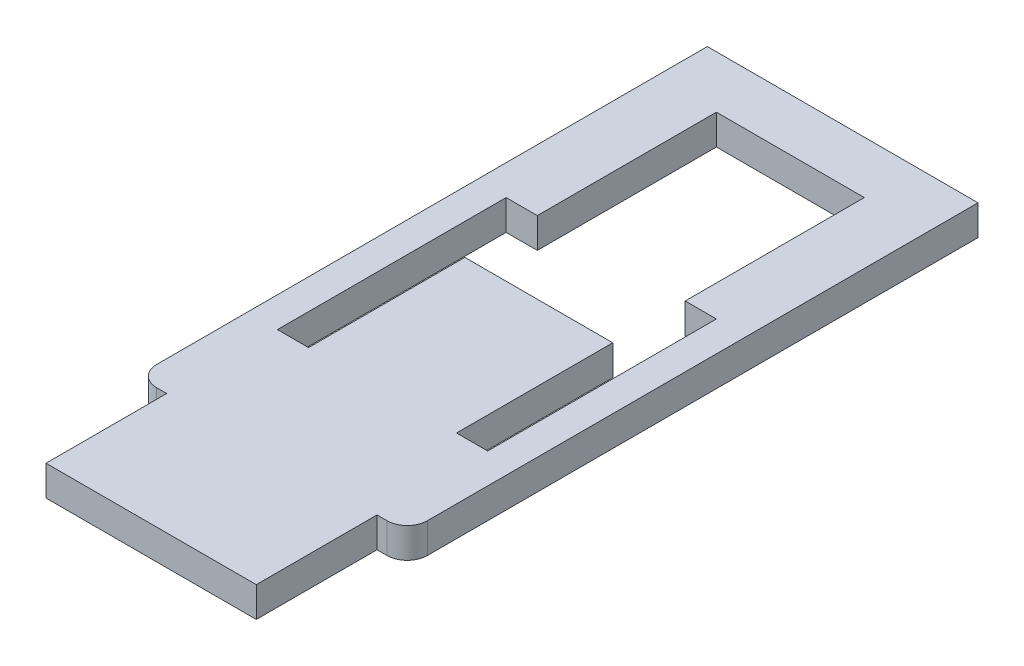
SolidWorks part; units mm, degrees
ref_plane "Front Plane" through (0, 0, 0) normal (0, 0, 1) x (1, 0, 0)
ref_plane "Top Plane" through (0, 0, 0) normal (0, 1, 0) x (1, 0, 0)
ref_plane "Right Plane" through (0, 0, 0) normal (1, 0, 0) x (0, 0, -1)
sketch "Sketch1" plane through (0, 0, 0) normal (0, 1, 0) x (1, 0, 0)
  line L5 (-13.4502, -34.3657) -> (13.4503, -34.3657)
  line L6 (-13.4502, -34.3657) -> (-13.4502, 34.3657)
  line L11 (-13.4502, 34.3657) -> (13.4503, 34.3657)
  line L12 (13.4503, -34.3657) -> (13.4503, 34.3657)
  line L17 (-13.4502, -34.3657) -> (13.4503, 34.3657) construction
  line L18 (-13.4502, 34.3657) -> (13.4503, -34.3657) construction
  line L36 (-10.4502, -11.3656) -> (-7.3502, -11.3656)
  line L45 (-10.4502, -11.3656) -> (-10.4502, 11.3657)
  line L46 (-10.4502, 11.3657) -> (-7.3502, 11.3657)
  line L51 (-7.3502, -11.3656) -> (-7.3502, 11.3657)
  line L52 (-10.4502, -11.3656) -> (-7.3502, 11.3657) construction
  line L57 (-10.4502, 11.3657) -> (-7.3502, -11.3656) construction
  line L58 (10.4502, -11.3657) -> (7.3502, -11.3657)
  line L63 (10.4502, -11.3657) -> (10.4502, 11.3656)
  line L64 (10.4502, 11.3656) -> (7.3502, 11.3656)
  line L65 (7.3502, -11.3657) -> (7.3502, 11.3656)
  line L66 (10.4502, -11.3657) -> (7.3502, 11.3656) construction
  line L67 (-7.3502, 4.1657) -> (7.3502, 4.1657)
  line L68 (-7.3502, 4.1657) -> (-7.3502, 29.1657)
  line L69 (-7.3502, 29.1657) -> (7.3502, 29.1657)
  line L70 (7.3502, 4.1657) -> (7.3502, 29.1657)
  line L71 (-7.3502, 4.1657) -> (7.3502, 29.1657) construction
  line L72 (-7.3502, 29.1657) -> (7.3502, 4.1657) construction
  line L73 (10.4502, 11.3656) -> (7.3502, -11.3657) construction
  line L74 (-10.4502, -34.3657) -> (-13.4503, -34.3657)
  line L75 (-10.4502, -34.3657) -> (-10.4502, -22.3657)
  line L76 (-10.4502, -22.3657) -> (-13.4502, -22.3657)
  line L77 (-13.4503, -34.3657) -> (-13.4502, -22.3657)
  line L78 (-10.4502, -34.3657) -> (-13.4502, -22.3657) construction
  line L79 (-10.4502, -22.3657) -> (-13.4503, -34.3657) construction
  line L80 (10.4502, -22.3657) -> (13.4503, -22.3657)
  line L81 (10.4502, -22.3657) -> (10.4503, -34.3657)
  line L82 (10.4503, -34.3657) -> (13.4503, -34.3657)
  line L83 (13.4503, -22.3657) -> (13.4503, -34.3657)
  line L84 (10.4502, -22.3657) -> (13.4503, -34.3657) construction
  line L85 (10.4503, -34.3657) -> (13.4503, -22.3657) construction
  point P0 (0, 0)
  point P5 (-8.9003, 0)
  point P6 (0, 0)
  point P7 (8.9002, 0)
  point P13 (-11.9502, -28.3657)
  point P21 (11.9502, -28.3656)
  point P24 (0, 16.6657)
  dimension "D1" = 5.2
  dimension "D2" = 14.7005
  dimension "D3" = 68.7313
  dimension "D4" = 3.1
  dimension "D5" = 22.7313
  dimension "D6" = 3
  dimension "D7" = 25
  dimension "D8" = 3
  dimension "D9" = 12
extrude "Boss-Extrude1" add sketch "Sketch1" along normal blind 3
fillet "Fillet1" radius 2 2 edges at (13.4503, 1.5, 22.3657) (-13.4502, 1.5, 22.3657)
